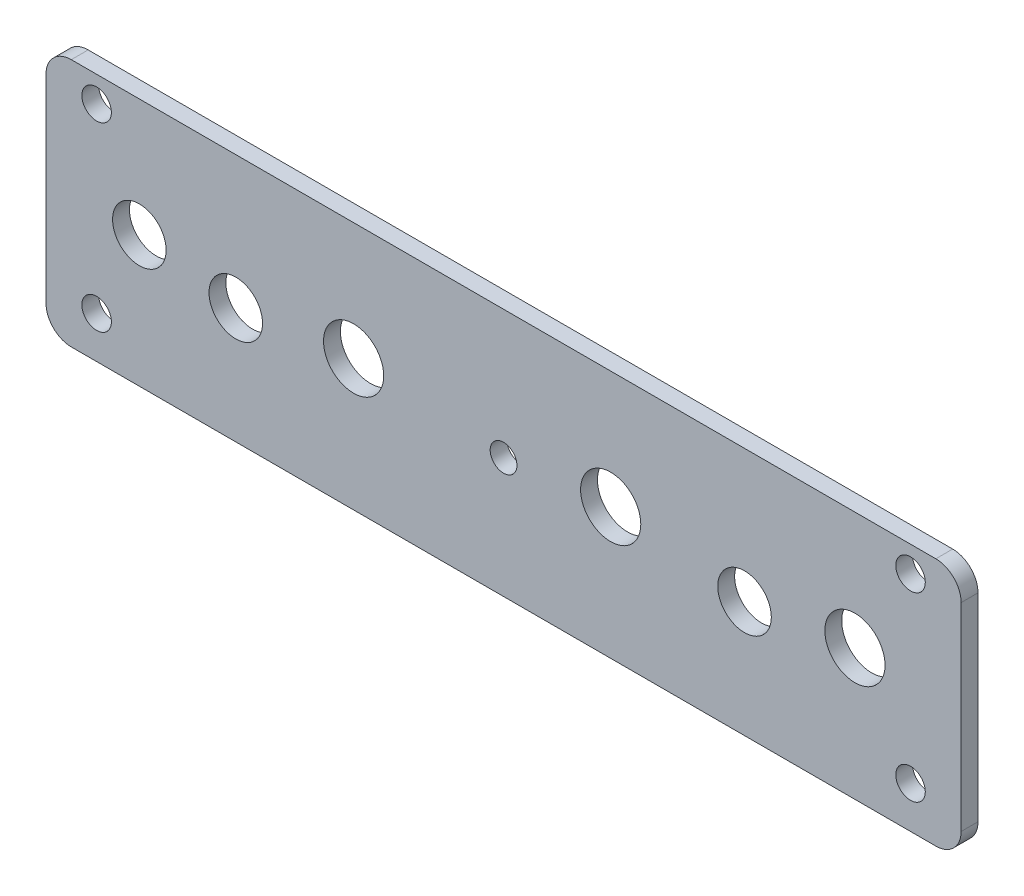
SolidWorks part; units mm, degrees
ref_plane "Front Plane" through (0, 0, 0) normal (0, 0, 1) x (1, 0, 0)
ref_plane "Top Plane" through (0, 0, 0) normal (0, 1, 0) x (1, 0, 0)
ref_plane "Right Plane" through (0, 0, 0) normal (1, 0, 0) x (0, 0, -1)
sketch "Sketch1" plane through (0, 0, 0) normal (0, 0, 1) x (1, 0, 0)
  line L0 (0, -55) -> (0, 55) construction
  line L1 (51.25, -14.75) -> (-51.25, -14.75)
  line L2 (54.25, -11.75) -> (54.25, 11.75)
  line L3 (51.25, 14.75) -> (-51.25, 14.75)
  line L4 (-54.25, -11.75) -> (-54.25, 11.75)
  line L5 (54.25, -14.75) -> (-54.25, 14.75) construction
  line L6 (54.25, 14.75) -> (-54.25, -14.75) construction
  line L7 (55, 0) -> (-55, 0) construction
  arc A0 (51.25, -14.75) -> (54.25, -11.75) centre (51.25, -11.75) ccw
  arc A1 (54.25, 11.75) -> (51.25, 14.75) centre (51.25, 11.75) ccw
  arc A2 (-51.25, -14.75) -> (-54.25, -11.75) centre (-51.25, -11.75) cw
  arc A3 (-51.25, 14.75) -> (-54.25, 11.75) centre (-51.25, 11.75) ccw
  circle A4 centre (0, -0.5) radius 1.5875
  circle A5 centre (-17.78, 0.8) radius 3.5687
  circle A6 centre (-31.75, -1) radius 3.175
  circle A7 centre (-43.18, 0.8) radius 3.175
  circle A8 centre (12.7, 0.8) radius 3.5687
  circle A9 centre (28.57, -1) radius 3.175
  circle A10 centre (41.66, 0.8) radius 3.5687
  circle A11 centre (48.25, 11.7) radius 1.75
  circle A12 centre (48.25, -9.8) radius 1.75
  circle A13 centre (-48.25, 11.7) radius 1.75
  circle A14 centre (-48.25, -9.8) radius 1.75
  point P0 (0, 0)
  dimension "D3" = 3
  dimension "D6" = 0.8
  dimension "D8" = 7.1374
  dimension "D9" = 1
  dimension "D10" = 0.8
  dimension "D11" = 6.35
  dimension "D13" = 12.7
  dimension "D15" = 7.1374
  dimension "D16" = 28.57
  dimension "D18" = 6.35
  dimension "D19" = 0.8
  dimension "D21" = 7.1374
  dimension "D1" = 29.5
  dimension "D2" = 108.5
  dimension "D7" = 17.78
  dimension "D12" = 43.18
  dimension "D14" = 0.8
  dimension "D17" = 1
  dimension "D20" = 41.66
extrude "Boss-Extrude1" add sketch "Sketch1" along normal blind 2
